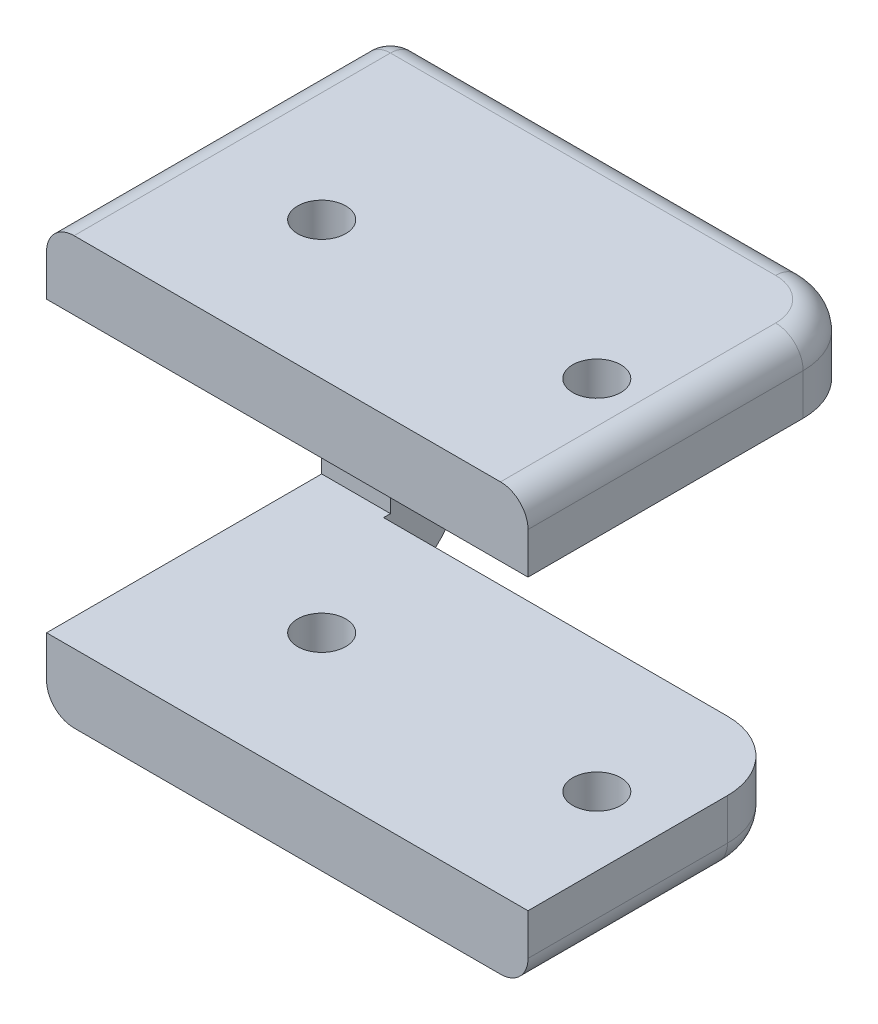
SolidWorks part; units mm, degrees
ref_plane "Front Plane" through (0, 0, 0) normal (0, 0, 1) x (1, 0, 0)
ref_plane "Top Plane" through (0, 0, 0) normal (0, 1, 0) x (1, 0, 0)
ref_plane "Right Plane" through (0, 0, 0) normal (1, 0, 0) x (0, 0, -1)
sketch "Sketch1" plane through (0, 0, 0) normal (0, 1, 0) x (1, 0, 0)
  line L0 (-15, 7.5) -> (15, 7.5) construction
  line L1 (-15, 12.5) -> (15, 12.5)
  line L2 (-15, 12.5) -> (-15, -12.5)
  line L3 (-15, -12.5) -> (15, -12.5)
  line L4 (15, 12.5) -> (15, -12.5)
  line L5 (-15, 12.5) -> (15, -12.5) construction
  line L6 (-15, -12.5) -> (15, 12.5) construction
  line L7 (-10, 7.5) -> (-10, -12.5) construction
  line L8 (10, 7.5) -> (10, -12.5) construction
  circle A0 centre (-10, -2.5) radius 1.75
  circle A1 centre (10, -2.5) radius 1.75
  point P0 (0, 0)
  dimension "D3" = 3.5
  dimension "D4" = 3.5
  dimension "D1" = 25
  dimension "D2" = 20
  dimension "D5" = 5
  dimension "D6" = 5
  dimension "D7" = 30
extrude "Boss-Extrude1" add sketch "Sketch1" along normal blind 5
sketch "Sketch2" plane through (-15, 0, 0) normal (-1, 0, 0) x (0, 0, 1)
  line L0 (12.5, 5) -> (12.5, 0) construction
  line L1 (-12.5, 5) -> (12.5, 5)
  line L2 (-12.5, 5) -> (-12.5, -26)
  line L3 (-12.5, -26) -> (12.5, -26)
  line L4 (12.5, 5) -> (12.5, 0)
  line L5 (-12.5, 0) -> (12.5, 0) construction
  line L6 (12.5, -21) -> (-7.5, -21)
  line L8 (12.5, 0) -> (-7.5, 0)
  line L9 (-7.5, -21) -> (-7.5, 0)
  line L10 (12.5, -21) -> (12.5, -26)
  dimension "D1" = 31
  dimension "D2" = 20
  dimension "D3" = 21
extrude "Boss-Extrude2" add sketch "Sketch2" along normal blind 5
sketch "Sketch3" plane through (-15, 0, 0) normal (1, 0, 0) x (0, 0, -1)
  line L1 (-12.5, -26) -> (7, -26)
  line L2 (-12.5, -26) -> (-12.5, -21)
  line L3 (-12.5, -21) -> (7, -21)
  line L4 (7, -26) -> (7, -21)
  line L5 (7.5, -21) -> (7.5, 0) construction
  dimension "D1" = 0.5
extrude "Boss-Extrude3" add sketch "Sketch3" along normal blind 30
sketch "Sketch4" plane through (0, -26, 0) normal (0, -1, 0) x (1, 0, 0)
  circle A0 centre (-10, 2.5) radius 1.75
  circle A1 centre (10, 2.5) radius 1.75
  circle A2 centre (-10, 2.5) radius 1.75 construction
  circle A3 centre (10, 2.5) radius 1.75 construction
  dimension "D1" = 3.5
  dimension "D2" = 3.5
extrude "Cut-Extrude1" cut sketch "Sketch4" against normal through all
fillet "Fillet1" radius 5 3 edges at (-17.5, -26, -12.5) (15, -23.5, -7) (15, 2.5, -12.5)
fillet "Fillet2" radius 2 10 edges at (15, -26, 5.25) (13.5355, -26, -5.5355) (-20, -26, 2.5) (-20, -24.5355, -11.0355) (-5, 5, -12.5) (13.5355, 5, -11.0355) (-2.5, -26, -7) (-20, -8, -12.5) (15, 5, 2.5) (-20, 5, 0)
